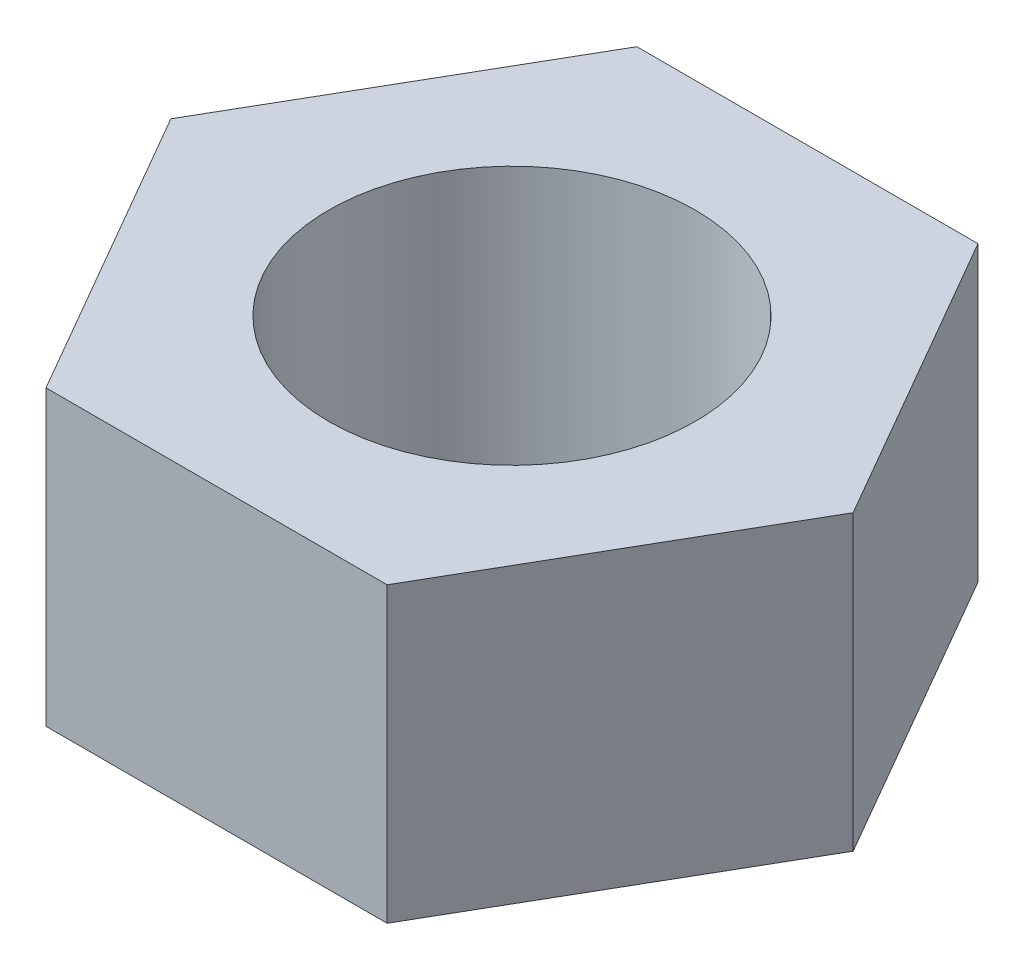
SolidWorks part; units mm, degrees
ref_plane "Front Plane" through (0, 0, 0) normal (0, 0, 1) x (1, 0, 0)
ref_plane "Top Plane" through (0, 0, 0) normal (0, 1, 0) x (1, 0, 0)
ref_plane "Right Plane" through (0, 0, 0) normal (1, 0, 0) x (0, 0, -1)
sketch "Sketch1" plane through (0, 0, 0) normal (0, 1, 0) x (1, 0, 0)
  line L1 (3.7239, 6.45) -> (-3.7239, 6.45)
  line L2 (-3.7239, 6.45) -> (-7.4478, 0)
  line L3 (-7.4478, 0) -> (-3.7239, -6.45)
  line L4 (-3.7239, -6.45) -> (3.7239, -6.45)
  line L5 (3.7239, -6.45) -> (7.4478, 0)
  line L6 (7.4478, 0) -> (3.7239, 6.45)
  circle A0 centre (0, 0) radius 6.45 construction
  circle A1 centre (0, 0) radius 4
  dimension "D2" = 8
  dimension "D1" = 12.9
extrude "Boss-Extrude1" add sketch "Sketch1" along normal blind 6.4
